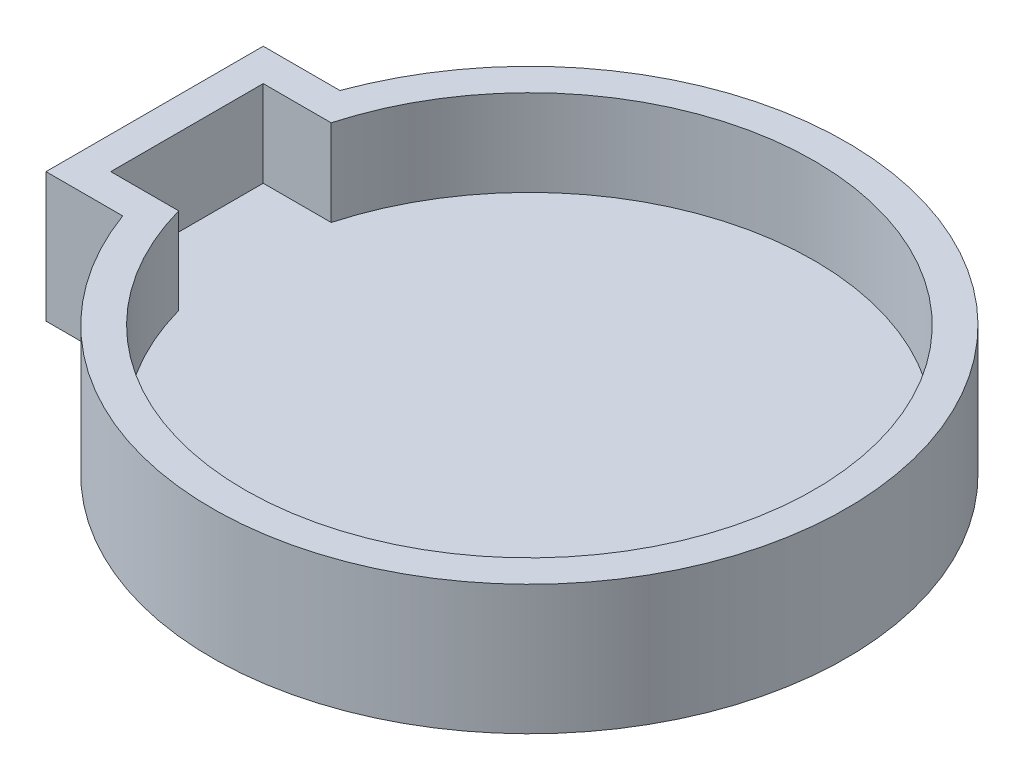
SolidWorks part; units mm, degrees
ref_plane "정면" through (0, 0, 0) normal (0, 0, 1) x (1, 0, 0)
ref_plane "윗면" through (0, 0, 0) normal (0, 1, 0) x (1, 0, 0)
ref_plane "우측면" through (0, 0, 0) normal (1, 0, 0) x (0, 0, -1)
sketch "스케치1" plane through (0, 0, 0) normal (0, 1, 0) x (1, 0, 0)
  line L0 (-26.05, 7.55) -> (-20.7171, 7.55)
  line L1 (-24.05, 5.55) -> (-19.2666, 5.55) construction
  line L2 (-24.05, 5.55) -> (-24.05, -5.55) construction
  line L3 (-24.05, -5.55) -> (-19.2666, -5.55) construction
  line L4 (-26.05, -7.55) -> (-20.7171, -7.55)
  line L5 (-26.05, 7.55) -> (-26.05, -7.55)
  arc A0 (-19.2666, -5.55) -> (-19.2666, 5.55) centre (0, 0) ccw construction
  arc A1 (-20.7171, -7.55) -> (-20.7171, 7.55) centre (0, 0) ccw
  point P8 (-24.05, 0)
  dimension "D1" = 40.1
  dimension "D2" = 11.1
  dimension "D3" = 24.05
  dimension "D4" = 2
extrude "보스-돌출1" add sketch "스케치1" along normal blind 3
sketch "스케치2" plane through (0, 3, 0) normal (0, 1, 0) x (1, 0, 0)
  line L0 (-19.0775, 5.3) -> (-23.8, 5.3)
  line L1 (-23.8, 5.3) -> (-23.8, -5.3)
  line L2 (-23.8, -5.3) -> (-19.0775, -5.3)
  line L3 (-26.05, 7.55) -> (-26.05, -7.55)
  line L4 (-26.05, -7.55) -> (-20.7171, -7.55)
  line L5 (-20.7171, 7.55) -> (-26.05, 7.55)
  line L6 (-26.05, 7.55) -> (-26.05, -7.55)
  line L7 (-26.05, -7.55) -> (-20.7171, -7.55)
  line L8 (-20.7171, 7.55) -> (-26.05, 7.55)
  arc A0 (-19.0775, -5.3) -> (-19.0775, 5.3) centre (0, 0) ccw
  arc A1 (-20.7171, -7.55) -> (-20.7171, 7.55) centre (0, 0) ccw
  arc A2 (-20.7171, -7.55) -> (-20.7171, 7.55) centre (0, 0) ccw
  dimension "D1" = 0
  dimension "D2" = 2.25
extrude "보스-돌출2" add sketch "스케치2" along normal blind 6
ref_plane "평면1" through (0, -20, 0) normal (0, -1, 0) x (-1, 0, 0)
